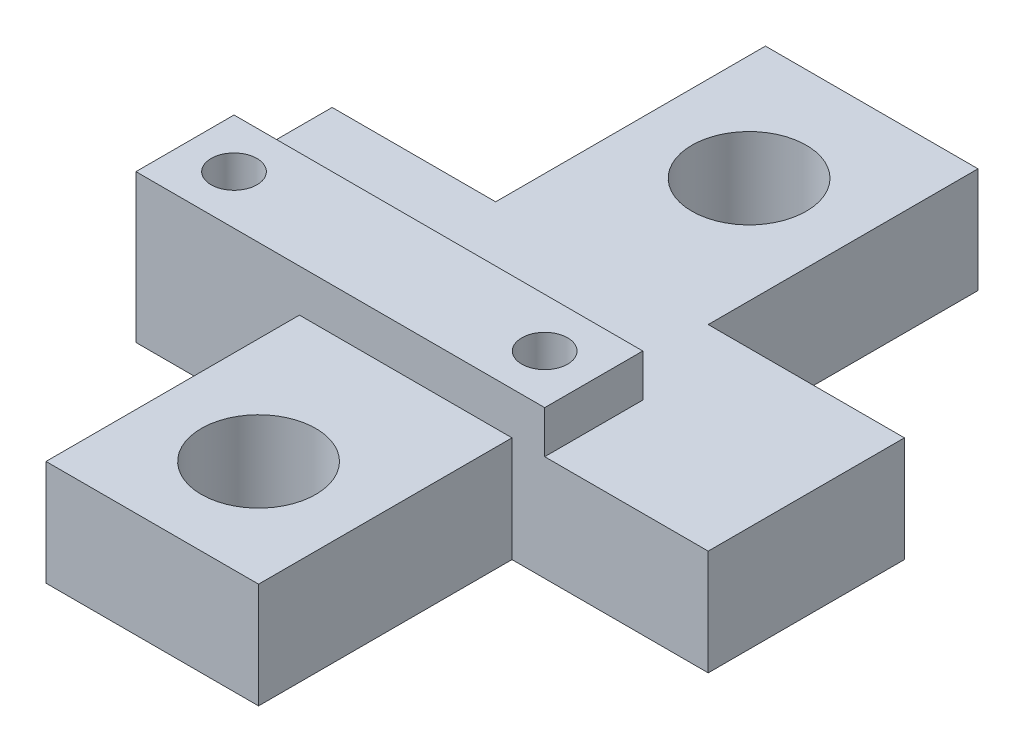
SolidWorks part; units mm, degrees
ref_plane "Front" through (0, 0, 0) normal (0, 0, 1) x (1, 0, 0)
ref_plane "Top" through (0, 0, 0) normal (0, 1, 0) x (1, 0, 0)
ref_plane "Right" through (0, 0, 0) normal (1, 0, 0) x (0, 0, -1)
sketch "Sketch1" plane through (0, 0, 0) normal (0, 1, 0) x (1, 0, 0)
  line L0 (5.5, 6) -> (5.5, 22.5)
  line L1 (-17.5, -6) -> (-7.5, -6)
  line L2 (-17.5, -6) -> (-17.5, 6)
  line L3 (-17.5, 6) -> (-7.5, 6)
  line L4 (17.5, -6) -> (17.5, 6)
  line L5 (-17.5, 0) -> (17.5, 0) construction
  line L7 (-7.5, -21.5) -> (5.5, -21.5)
  line L8 (-7.5, -21.5) -> (-7.5, -6)
  line L9 (-7.5, 22.5) -> (5.5, 22.5)
  line L10 (5.5, -21.5) -> (5.5, -6)
  line L13 (-7.5, 6) -> (-7.5, 22.5)
  line L14 (5.5, 6) -> (17.5, 6)
  line L17 (5.5, -6) -> (17.5, -6)
  dimension "D1" = 12
  dimension "D2" = 35
  dimension "D3" = 44
  dimension "D4" = 13
  dimension "D5" = 10
  dimension "D6" = 16.5
extrude "Boss-Extrude1" add sketch "Sketch1" along normal blind 6.45
sketch "Sketch2" plane through (0, 6.45, 0) normal (0, 1, 0) x (1, 0, 0)
  line L0 (-17.5, 6) -> (-17.5, -6) construction
  line L1 (-17.5, 0) -> (7.5, 0)
  line L2 (-17.5, 0) -> (-17.5, -6)
  line L3 (-17.5, -6) -> (7.5, -6)
  line L4 (7.5, 0) -> (7.5, -6)
  line L5 (-17.5, 0) -> (7.5, -6) construction
  line L6 (-17.5, -6) -> (7.5, 0) construction
  line L7 (-17.5, -6) -> (-7.5, -6) construction
  point P0 (-5, -3)
  dimension "D1" = 6
  dimension "D2" = 25
extrude "Boss-Extrude2" add sketch "Sketch2" along normal blind 2.6
sketch "Sketch3" plane through (0, 6.45, 0) normal (0, 1, 0) x (1, 0, 0)
  line L0 (5.5, 22.5) -> (-7.5, 22.5) construction
  line L1 (-1, 22.5) -> (-1, -21.5) construction
  line L2 (-7.5, -21.5) -> (5.5, -21.5) construction
  circle A0 centre (-1, 15) radius 3.5
  circle A1 centre (-1, -15) radius 3.5
  dimension "D1" = 7
  dimension "D2" = 7.5
  dimension "D3" = 6.5
extrude "Cut-Extrude1" cut sketch "Sketch3" against normal through all
sketch "Sketch4" plane through (0, 9.05, 0) normal (0, 1, 0) x (1, 0, 0)
  line L0 (-17.5, 0) -> (-17.5, -6) construction
  line L1 (7.5, -6) -> (7.5, 0) construction
  line L2 (7.5, 0) -> (-17.5, 0) construction
  circle A0 centre (-14.5, -3) radius 1.4
  circle A1 centre (4.5, -3) radius 1.4
  dimension "D1" = 2.8
  dimension "D2" = 3
  dimension "D3" = 3
  dimension "D4" = 3
extrude "Cut-Extrude2" cut sketch "Sketch4" against normal through all
